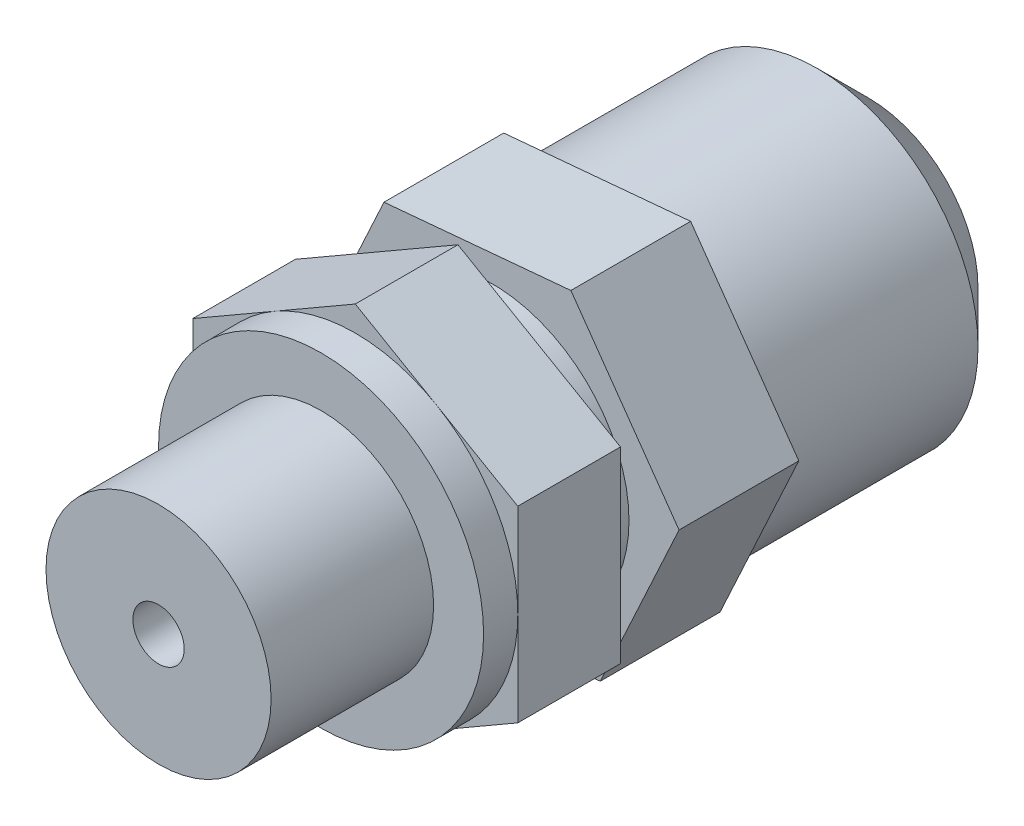
SolidWorks part; units mm, degrees
ref_plane "Plane1" through (0, 0, 0) normal (0, 0, 1) x (1, 0, 0)
ref_plane "Plane2" through (0, 0, 0) normal (0, 1, 0) x (1, 0, 0)
ref_plane "Plane3" through (0, 0, 0) normal (1, 0, 0) x (0, 0, -1)
sketch "Sketch1" plane through (0, 0, 0) normal (0, 0, 1) x (1, 0, 0)
  line L1 (0, 10.9697) -> (-9.5, 5.4848)
  line L2 (-9.5, 5.4848) -> (-9.5, -5.4848)
  line L3 (-9.5, -5.4848) -> (0, -10.9697)
  line L4 (0, -10.9697) -> (9.5, -5.4848)
  line L5 (9.5, -5.4848) -> (9.5, 5.4848)
  line L6 (9.5, 5.4848) -> (0, 10.9697)
  circle A0 centre (0, 0) radius 9.5 construction
  dimension "Nøglevidde1" = 19
extrude "Base-Extrude" add sketch "Sketch1" along normal blind 6
sketch "Sketch2" plane through (0, 0, 6) normal (0, 0, 1) x (1, 0, 0)
  circle A0 centre (0, 0) radius 9.5
  dimension "Nøgledia.1" = 19
extrude "Boss-Extrude1" add sketch "Sketch2" along normal blind 2
sketch "Sketch3" plane through (0, 0, 8) normal (0, 0, 1) x (1, 0, 0)
  circle A0 centre (0, 0) radius 6.5785
  dimension "Gev./dia." = 13.157
extrude "Boss-Extrude2" add sketch "Sketch3" along normal blind 9.5
sketch "Sketch4" plane through (0, 0, 17.5) normal (0, 0, 1) x (1, 0, 0)
  circle A0 centre (0, 0) radius 1.5
  dimension "Indv. dia." = 3
extrude "Cut-Extrude1" cut sketch "Sketch4" against normal blind 9.5
sketch "Sketch5" plane through (0, 0, 0) normal (0, 0, -1) x (-1, 0, 0)
  circle A0 centre (0, 0) radius 8
  dimension "Nøgle.dia.2" = 16
extrude "Boss-Extrude3" add sketch "Sketch5" along normal blind 2
sketch "Sketch7" plane through (0, 0, -2) normal (0, 0, -1) x (-1, 0, 0)
  line L1 (10.9246, -0.9931) -> (6.3224, 8.9644)
  line L2 (6.3224, 8.9644) -> (-4.6022, 9.9576)
  line L3 (-4.6022, 9.9576) -> (-10.9246, 0.9931)
  line L4 (-10.9246, 0.9931) -> (-6.3224, -8.9644)
  line L5 (-6.3224, -8.9644) -> (4.6022, -9.9576)
  line L6 (4.6022, -9.9576) -> (10.9246, -0.9931)
  circle A0 centre (0, 0) radius 9.5 construction
  dimension "Nøglevidde2" = 19
extrude "Boss-Extrude4" add sketch "Sketch7" along normal blind 7
sketch "Sketch8" plane through (0, 0, -9) normal (0, 0, -1) x (-1, 0, 0)
  circle A0 centre (0, 0) radius 9.4
  dimension "Topdia." = 18.8
extrude "Boss-Extrude5" add sketch "Sketch8" along normal blind 15
chamfer "Chamfer1" distance 3 angle 45 1 edges at (-9.4, 0, -24)
ref_plane "Plane4" [suppressed] through (0, 0, 14.5) normal (0, 0, 1) x (1, 0, 0)
sketch "Sketch9" [suppressed] plane through (0, 0, 14.5) normal (0, 0, 1) x (1, 0, 0)
  line L1 (11, -6.3509) -> (11, 6.3509)
  line L2 (11, 6.3509) -> (0, 12.7017)
  line L3 (0, 12.7017) -> (-11, 6.3509)
  line L4 (-11, 6.3509) -> (-11, -6.3509)
  line L5 (-11, -6.3509) -> (0, -12.7017)
  line L6 (0, -12.7017) -> (11, -6.3509)
  circle A0 centre (0, 0) radius 11 construction
  circle A1 centre (0, 0) radius 6.5785 construction
  circle A2 centre (0, 0) radius 6.5785
  dimension "D1" = 22
extrude "Boss-Extrude6" [suppressed] add sketch "Sketch9" along normal blind 16
sketch "Sketch10" [suppressed] plane through (0, 0, 30.5) normal (0, 0, 1) x (1, 0, 0)
  circle A0 centre (0, 0) radius 6.5785 construction
  circle A1 centre (0, 0) radius 6.5785
  circle A2 centre (0, 0) radius 8.25
  dimension "D1" = 16.5
extrude "Cut-Extrude2" [suppressed] cut sketch "Sketch10" against normal blind 10
